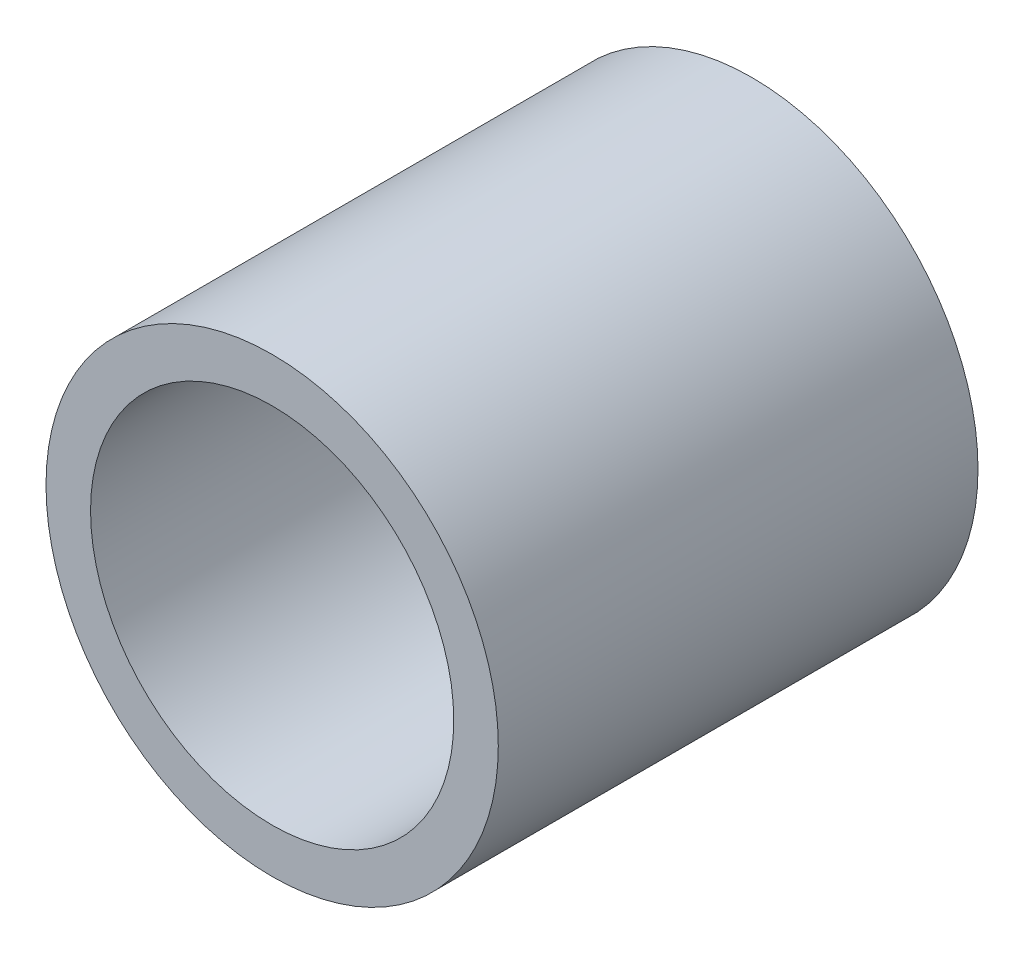
SolidWorks part; units mm, degrees
ref_plane "Front Plane" through (0, 0, 0) normal (0, 0, 1) x (1, 0, 0)
ref_plane "Top Plane" through (0, 0, 0) normal (0, 1, 0) x (1, 0, 0)
ref_plane "Right Plane" through (0, 0, 0) normal (1, 0, 0) x (0, 0, -1)
sketch "Sketch1" plane through (0, 0, 0) normal (0, 0, 1) x (1, 0, 0)
  circle A0 centre (0, 0) radius 16.5
extrude "Boss-Extrude1" add sketch "Sketch1" along normal blind 35 contours A0
sketch "Sketch2" plane through (0, 0, 0) normal (0, 0, -1) x (-1, 0, 0)
  circle A0 centre (0, 0) radius 13.25
extrude "Cut-Extrude1" cut sketch "Sketch2" against normal up to surface (35 mm away) up to face at (16.5, 0, 35)
